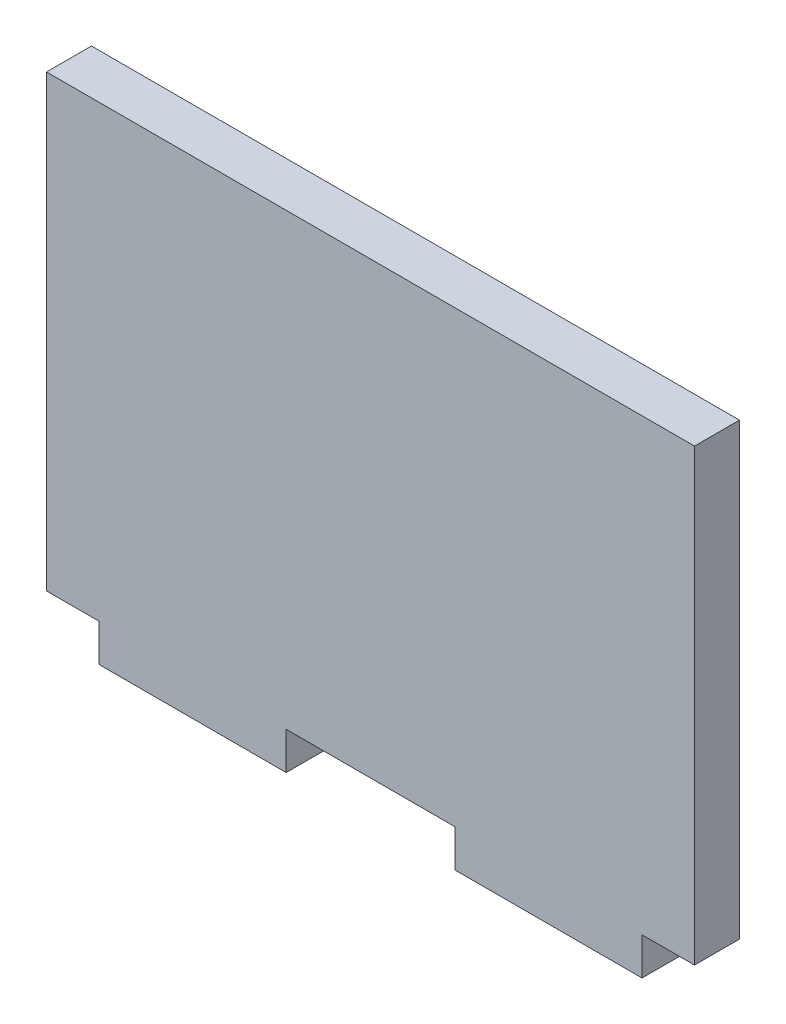
SolidWorks part; units mm, degrees
ref_plane "Plan de face" through (0, 0, 0) normal (0, 0, 1) x (1, 0, 0)
ref_plane "Plan de dessus" through (0, 0, 0) normal (0, 1, 0) x (1, 0, 0)
ref_plane "Plan de droite" through (0, 0, 0) normal (1, 0, 0) x (0, 0, -1)
sketch "Esquisse1" plane through (0, 0, 0) normal (0, 0, 1) x (1, 0, 0)
  line L1 (-26.5131, 55.7692) -> (59.9869, 55.7692)
  line L2 (-26.5131, 55.7692) -> (-26.5131, -4.2308)
  line L3 (-26.5131, -4.2308) -> (59.9869, -4.2308)
  line L4 (59.9869, 55.7692) -> (59.9869, -4.2308)
  line L5 (-19.5031, -4.2308) -> (5.4769, -4.2308)
  line L6 (-19.5031, -4.2308) -> (-19.5031, -9.2308)
  line L7 (-19.5031, -9.2308) -> (5.4769, -9.2308)
  line L8 (5.4769, -4.2308) -> (5.4769, -9.2308)
  line L9 (27.9969, -4.2308) -> (52.9769, -4.2308)
  line L10 (27.9969, -4.2308) -> (27.9969, -9.2308)
  line L11 (27.9969, -9.2308) -> (52.9769, -9.2308)
  line L12 (52.9769, -4.2308) -> (52.9769, -9.2308)
  dimension "D1" = 5
  dimension "D2" = 5
  dimension "D3" = 24.98
  dimension "D4" = 24.98
  dimension "D5" = 22.52
  dimension "D6" = 86.5
  dimension "D7" = 7.01
  dimension "D8" = 60
extrude "Boss.-Extru.1" add sketch "Esquisse1" along normal blind 6 contours L4 L1 L2 L3 | L8 L3 L6 L7 | L12 L3 L10 L11
